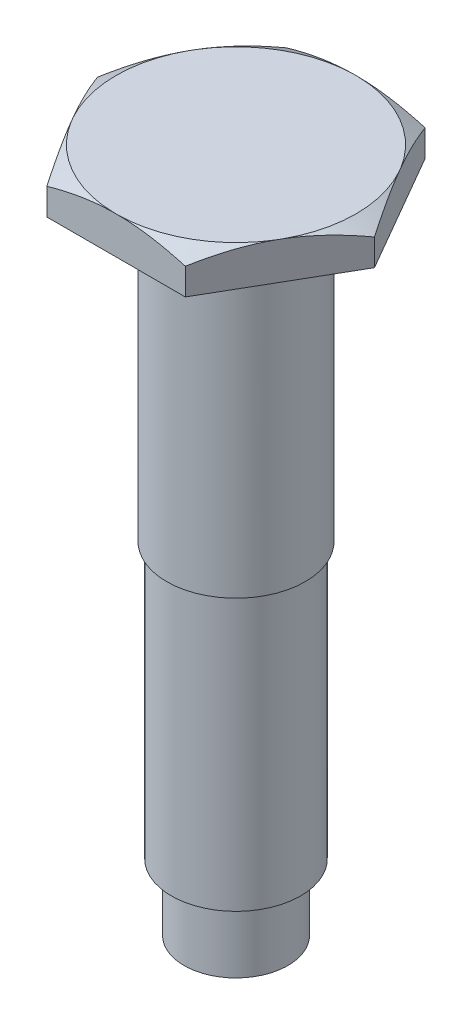
SolidWorks part; units mm, degrees
material "Plain Carbon Steel"
ref_plane "Front Plane" through (0, 0, 0) normal (0, 0, 1) x (1, 0, 0)
ref_plane "Top Plane" through (0, 0, 0) normal (0, 1, 0) x (1, 0, 0)
ref_plane "Right Plane" through (0, 0, 0) normal (1, 0, 0) x (0, 0, -1)
sketch "Sketch1" plane through (0, 0, 0) normal (0, 1, 0) x (1, 0, 0)
  line L1 (5.195, 0) -> (2.5975, 4.499)
  line L2 (2.5975, 4.499) -> (-2.5975, 4.499)
  line L3 (-2.5975, 4.499) -> (-5.195, 0)
  line L4 (-5.195, 0) -> (-2.5975, -4.499)
  line L5 (-2.5975, -4.499) -> (2.5975, -4.499)
  line L6 (2.5975, -4.499) -> (5.195, 0)
  circle A0 centre (0, 0) radius 4.499 construction
  dimension "D2" = 8.998
  dimension "D1" = 5.195
extrude "Boss-Extrude1" add sketch "Sketch1" along normal blind 1.4
sketch "Sketch2" plane through (0, 1.4, 0) normal (0, 1, 0) x (1, 0, 0)
  circle A0 centre (0, 0) radius 4.5
  dimension "D1" = 9
extrude "Cut-Extrude1" cut sketch "Sketch2" against normal blind 1 draft 60 flip side to cut contours A0
sketch "Sketch3" plane through (0, 0, 0) normal (0, -1, 0) x (1, 0, 0)
  circle A0 centre (0, 0) radius 2.425
  dimension "D1" = 4.85
extrude "Boss-Extrude2" add sketch "Sketch3" along normal blind 24.3
cosmetic thread "Cosmetic Thread1" parameters "D1"=10.3, "D2"=4.11
sketch "Sketch4" plane through (0, -24.3, 0) normal (0, -1, 0) x (1, 0, 0)
  circle A0 centre (0, 0) radius 1.95
  dimension "D1" = 3.9
extrude "Cut-Extrude2" cut sketch "Sketch4" against normal blind 2.5 flip side to cut
sketch "Sketch5" plane through (0, 0, 0) normal (0, -1, 0) x (1, 0, 0)
  circle A0 centre (0, 0) radius 2.6
  dimension "D1" = 5.2
extrude "Boss-Extrude3" add sketch "Sketch5" along normal blind 11.5
